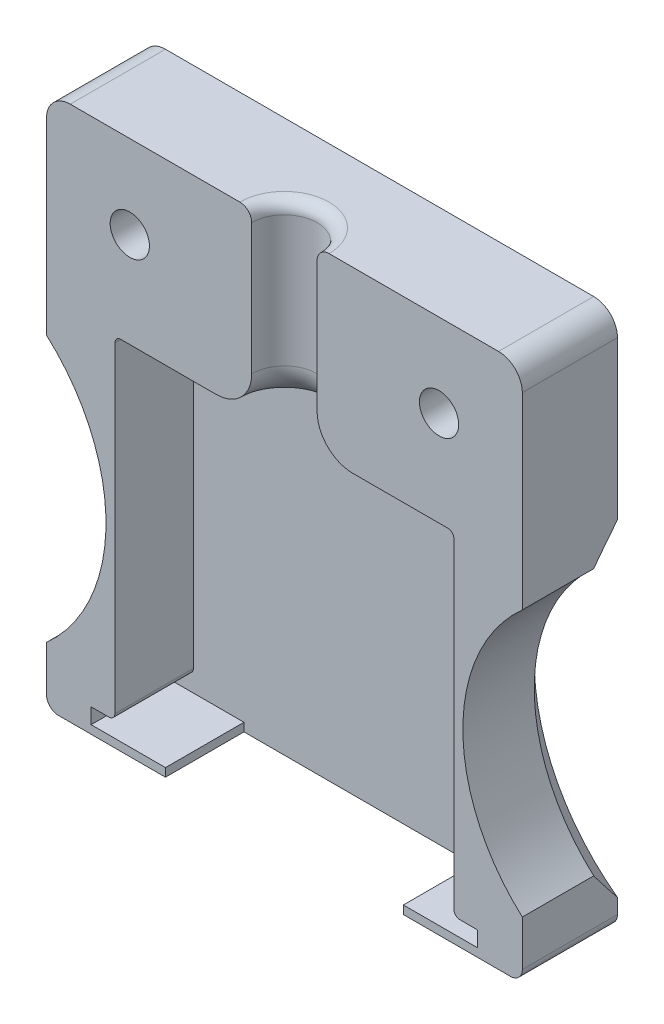
SolidWorks part; units mm, degrees
ref_plane "Alzado" through (0, 0, 0) normal (0, 0, 1) x (1, 0, 0)
ref_plane "Planta" through (0, 0, 0) normal (0, 1, 0) x (1, 0, 0)
ref_plane "Vista lateral" through (0, 0, 0) normal (1, 0, 0) x (0, 0, -1)
sketch "Croquis1" plane through (0, 0, 0) normal (0, 0, 1) x (1, 0, 0)
  line L1 (20, -22.5) -> (-20, -22.5)
  line L2 (20, -22.5) -> (20, 22.5)
  line L3 (20, 22.5) -> (-20, 22.5)
  line L4 (-20, -22.5) -> (-20, 22.5)
  line L5 (20, -22.5) -> (-20, 22.5) construction
  line L6 (20, 22.5) -> (-20, -22.5) construction
  point P0 (0, 0)
  dimension "D1" = 40
  dimension "D2" = 45
extrude "Saliente-Extruir1" add sketch "Croquis1" along normal blind 8
sketch "Croquis2" plane through (0, 0, 8) normal (0, 0, 1) x (1, 0, 0)
  line L0 (-20, -22.5) -> (20, -22.5) construction
  line L1 (16.25, -21.8) -> (-16.25, -21.8)
  line L2 (16.25, -21.8) -> (16.25, -20.5)
  line L3 (16.25, -20.5) -> (-16.25, -20.5)
  line L4 (-16.25, -21.8) -> (-16.25, -20.5)
  line L5 (16.25, -21.8) -> (-16.25, -20.5) construction
  line L6 (16.25, -20.5) -> (-16.25, -21.8) construction
  point P0 (0, -21.15)
  point P9 (0, -22.5)
  dimension "D1" = 1.3
  dimension "D2" = 0.7
  dimension "D3" = 32.5
extrude "Cortar-Extruir1" cut sketch "Croquis2" against normal blind 6.6
sketch "Croquis3" plane through (0, 0, 8) normal (0, 0, 1) x (1, 0, 0)
  line L0 (-20, 22.5) -> (-20, -22.5) construction
  circle A0 centre (-30, -6.5) radius 15
  circle A1 centre (30, -6.5) radius 15
  dimension "D1" = 30
  dimension "D6" = 30
  dimension "D2" = 10
  dimension "D3" = 16
  dimension "D4" = 16
  dimension "D5" = 10
extrude "Cortar-Extruir2" cut sketch "Croquis3" against normal blind 10
chamfer "Chaflán1" distance 2 angle 45 2 edges at (15, -6.5, 0) (-15, -6.5, 0)
sketch "Croquis4" plane through (0, 0, 8) normal (0, 0, 1) x (1, 0, 0)
  line L0 (-14.25, -20.5) -> (-14.25, 7.5)
  line L1 (16.25, -20.5) -> (-16.25, -20.5) construction
  line L2 (-14.25, 7.5) -> (14.25, 7.5)
  line L3 (14.25, 7.5) -> (14.25, -20.5)
  line L4 (14.25, -20.5) -> (-14.25, -20.5)
  dimension "D1" = 2
  dimension "D2" = 2
  dimension "D3" = 28
extrude "Cortar-Extruir3" cut sketch "Croquis4" against normal blind 6.6
sketch "Croquis6" plane through (0, 22.5, 0) normal (0, 1, 0) x (1, 0, 0)
  line L0 (20, -8) -> (-20, -8) construction
  circle A0 centre (0, -8) radius 2.75
  dimension "D1" = 5.5
extrude "Cortar-Extruir4" cut sketch "Croquis6" against normal blind 16.6
sketch "Croquis7" plane through (0, 0, 8) normal (0, 0, 1) x (1, 0, 0)
  circle A1 centre (13, 15.5) radius 1.65
  circle A2 centre (-13, 15.5) radius 1.65
  dimension "D1" = 3.3
  dimension "D2" = 3.3
  dimension "D3" = 7
  dimension "D4" = 7
  dimension "D5" = 7
  dimension "D6" = 7
extrude "Cortar-Extruir5" cut sketch "Croquis7" against normal blind 16.6
sketch "Croquis8" plane through (0, 0, 0) normal (0, 0, -1) x (-1, 0, 0)
  circle A0 centre (13, 15.5) radius 4
  circle A2 centre (-13, 15.5) radius 4
  dimension "D1" = 8
  dimension "D3" = 8
extrude "Cortar-Extruir6" cut sketch "Croquis8" against normal blind 4
sketch "Croquis9" plane through (0, -22.5, 0) normal (0, -1, 0) x (-1, 0, 0)
  line L0 (10, -8) -> (10, -1.4)
  line L1 (20, -8) -> (-20, -8) construction
  line L2 (10, -1.4) -> (-10, -1.4)
  line L3 (-10, -1.4) -> (-10, -8)
  line L4 (-10, -8) -> (10, -8)
  dimension "D1" = 20
  dimension "D2" = 10
  dimension "D3" = 10
  dimension "D4" = 6.6
extrude "Cortar-Extruir7" cut sketch "Croquis9" against normal blind 4
fillet "Redondeo1" radius 1 1 edges at (0, 22.5, 5.25)
fillet "Redondeo2" radius 2 2 edges at (20, 22.5, 4) (-20, 22.5, 4)
fillet "Redondeo3" radius 1 2 edges at (20, -22.5, 4) (-20, -22.5, 4)
fillet "Redondeo4" radius 3 1 edges at (0, 7.5, 5.25)
fillet "Redondeo5" radius 0.5 2 edges at (-14.25, -20.5, 4.7) (14.25, -20.5, 4.7)
fillet "Redondeo6" radius 0.5 2 edges at (14.25, 7.5, 4.7) (-14.25, 7.5, 4.7)
